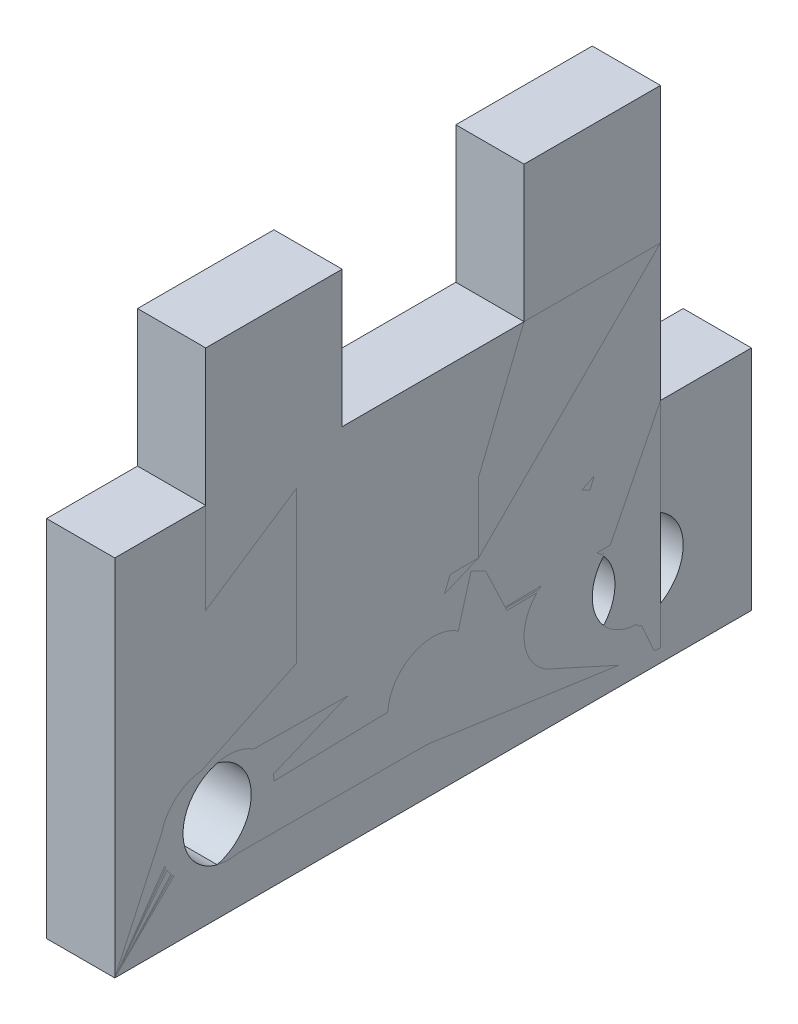
SolidWorks part; units mm, degrees
ref_plane "Front Plane" through (0, 0, 0) normal (0, 0, 1) x (1, 0, 0)
ref_plane "Top Plane" through (0, 0, 0) normal (0, 1, 0) x (1, 0, 0)
ref_plane "Right Plane" through (0, 0, 0) normal (1, 0, 0) x (0, 0, -1)
sketch "Sketch1" plane through (0, 0, 0) normal (0, 1, 0) x (1, 0, 0)
  line L0 (0, 0) -> (88.9, 0)
  dimension "D1" = 88.9
sketch "Sketch2" plane through (0, 0, 0) normal (0, 1, 0) x (1, 0, 0)
  line L0 (-10, 5) -> (10, 5)
  point P0 (10, 5)
  point P3 (0, 5)
  dimension "D1" = 20
  dimension "D2" = 5
sketch "Sketch3" plane through (0, 0, 0) normal (1, 0, 0) x (0, 0, -1)
  line L0 (0, 0) -> (120, 0)
  line L1 (120, 0) -> (120, 80)
  line L2 (120, 80) -> (80, 80)
  line L3 (80, 80) -> (80, 40)
  line L4 (80, 40) -> (40, 40)
  line L5 (40, 40) -> (40, 80)
  line L6 (40, 80) -> (0, 80)
  line L7 (0, 80) -> (0, 0)
  dimension "D1" = 120
  dimension "D2" = 80
  dimension "D3" = 40
  dimension "D4" = 40
  dimension "D5" = 40
extrude "Boss-Extrude1" add sketch "Sketch3" along normal blind 15
sketch "Sketch5" plane through (0, 0, 0) normal (-1, 0, 0) x (0, 0, 1)
  line L0 (-120, 20) -> (0, 20) construction
  line L1 (-120, 0) -> (-120, 80) construction
  line L2 (0, 80) -> (0, 0) construction
  line L3 (-100, 80) -> (-100, 0) construction
  line L4 (-120, 80) -> (-80, 80) construction
  line L5 (0, 0) -> (-120, 0) construction
  line L6 (-20, 80) -> (-20, 0) construction
  line L7 (-40, 80) -> (0, 80) construction
  circle A0 centre (-100, 20) radius 10
  circle A1 centre (-20, 20) radius 10
  dimension "D4" = 20
  dimension "D5" = 20
  dimension "D1" = 20
  dimension "D2" = 20
  dimension "D3" = 20
extrude "Cut-Extrude1" cut sketch "Sketch5" against normal blind 15
sketch "Sketch7" plane through (0, 0, 0) normal (1, 0, 0) x (0, 0, -1)
  line L0 (0, 0) -> (140, 0)
  line L1 (0, 0) -> (0, 60)
  line L2 (0, 60) -> (20, 60)
  line L3 (20, 60) -> (20, 110)
  line L4 (20, 110) -> (50, 110)
  line L5 (50, 110) -> (50, 80)
  line L6 (50, 80) -> (90, 80)
  line L7 (90, 80) -> (90, 110)
  line L8 (90, 110) -> (120, 110)
  line L9 (120, 110) -> (120, 50)
  line L10 (120, 50) -> (140, 50)
  line L11 (140, 50) -> (140, 0)
  line L12 (0, 20) -> (140, 20) construction
  line L13 (25, 0) -> (25, 110) construction
  line L14 (70, 0) -> (70, 80) construction
  line L15 (115, 0) -> (115, 110) construction
  circle A0 centre (25, 20) radius 10
  circle A1 centre (70, 20) radius 10
  circle A2 centre (115, 20) radius 10
  dimension "D14" = 20
  dimension "D15" = 20
  dimension "D16" = 20
  dimension "D1" = 140
  dimension "D2" = 60
  dimension "D3" = 110
  dimension "D4" = 80
  dimension "D5" = 50
  dimension "D6" = 20
  dimension "D7" = 50
  dimension "D8" = 120
  dimension "D9" = 40
  dimension "D10" = 20
  dimension "D11" = 25
  dimension "D12" = 45
  dimension "D13" = 45
extrude "Boss-Extrude2" add sketch "Sketch7" along normal blind 15 separate body
